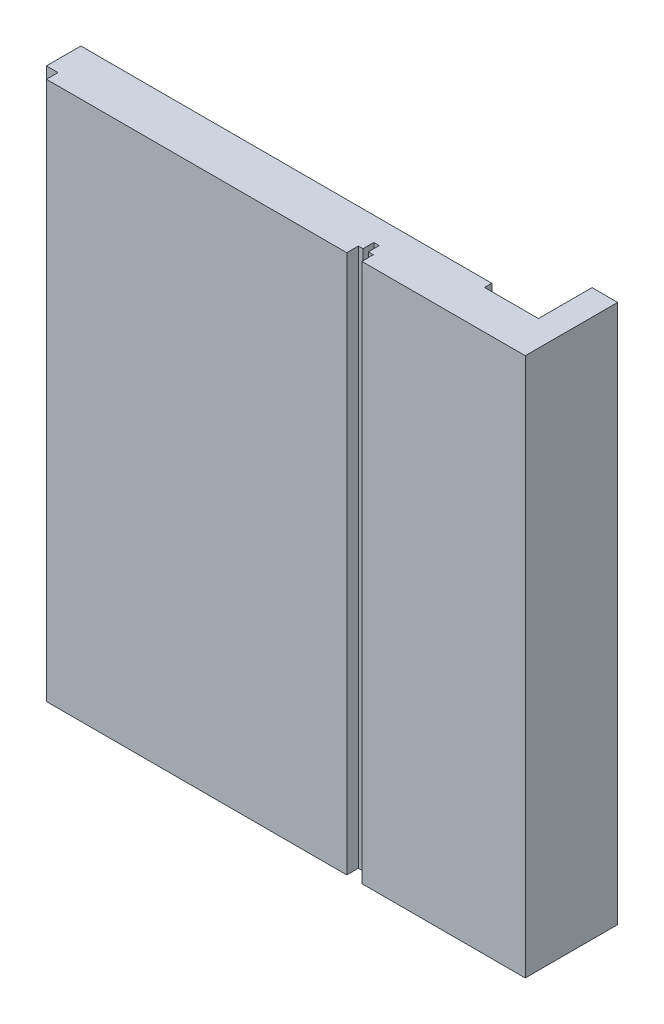
SolidWorks part; units mm, degrees
material "6061 Alloy"
ref_plane "Front Plane" through (0, 0, 0) normal (0, 0, 1) x (1, 0, 0)
ref_plane "Top Plane" through (0, 0, 0) normal (0, 1, 0) x (1, 0, 0)
ref_plane "Right Plane" through (0, 0, 0) normal (1, 0, 0) x (0, 0, -1)
sketch "Sketch1" plane through (0, 0, 0) normal (0, 1, 0) x (1, 0, 0)
  line L0 (-4.75, 15) -> (-4.75, 5.05)
  line L1 (-30.32, 0) -> (-31.25, 0)
  line L2 (0, 0) -> (0, 15)
  line L3 (0, 15) -> (-4.75, 15)
  line L4 (-91, 0) -> (-91, 6.4)
  line L5 (-4.75, 5.05) -> (-14.75, 5.05)
  line L6 (-14.75, 5.05) -> (-14.75, 6.4)
  line L7 (-14.75, 6.4) -> (-91, 6.4)
  line L8 (-32.25, 0) -> (-32.25, 2)
  line L9 (-32.25, 2) -> (-31.25, 2)
  line L10 (-31.25, 2) -> (-31.25, 0)
  line L11 (-32.25, 0) -> (-33.12, 0)
  line L13 (-88.85, -2.14) -> (-33.12, -2.14)
  line L14 (-33.12, -2.14) -> (-33.12, 0)
  line L15 (-30.32, 0) -> (-30.32, -2.14)
  line L16 (-30.32, -2.14) -> (0, -2.14)
  line L17 (0, -2.14) -> (0, 0)
  line L18 (-91, 0) -> (-88.85, 0)
  line L19 (-88.85, 0) -> (-88.85, -2.14)
  dimension "D1" = 91
  dimension "D2" = 6.4
  dimension "D3" = 1.35
  dimension "D4" = 15
  dimension "D5" = 4.75
  dimension "D6" = 10
  dimension "D7" = 1
  dimension "D8" = 31.25
  dimension "D9" = 2
  dimension "D10" = 30.32
  dimension "D11" = 8.54
  dimension "D12" = 2.15
  dimension "D13" = 55.73
extrude "Boss-Extrude1" add sketch "Sketch1" along normal blind 100
